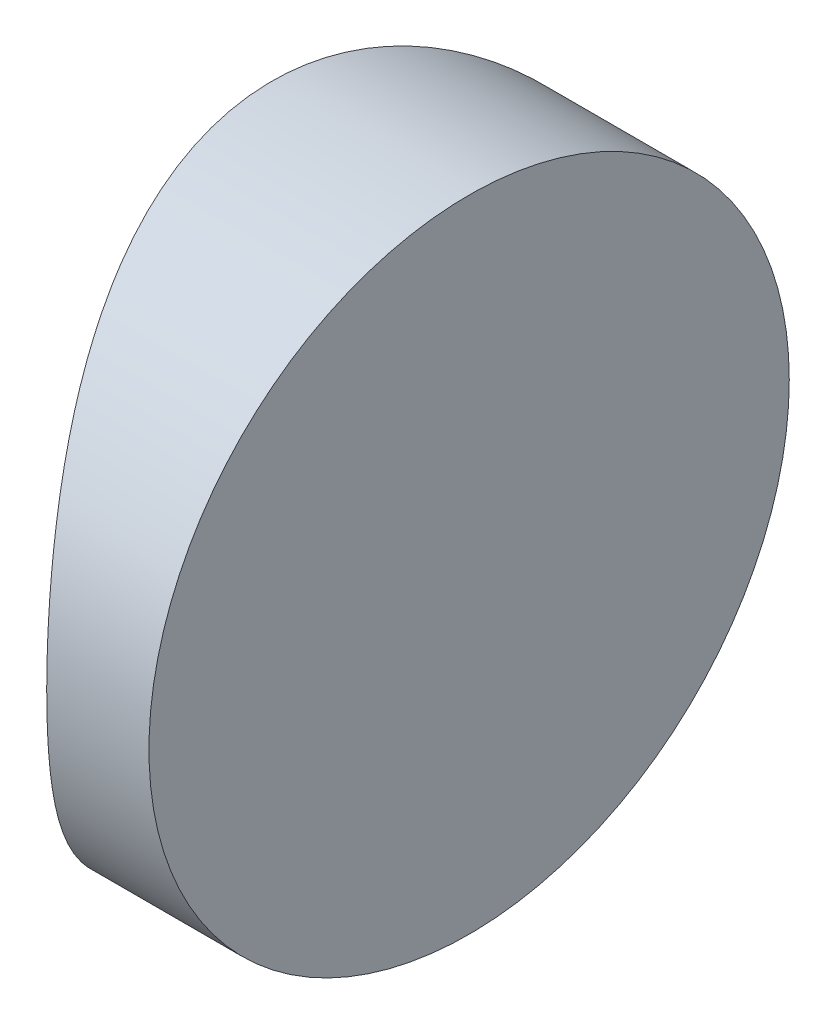
SolidWorks part; units mm, degrees
ref_plane "前视基准面" through (0, 0, 0) normal (0, 0, 1) x (1, 0, 0)
ref_plane "上视基准面" through (0, 0, 0) normal (0, 1, 0) x (1, 0, 0)
ref_plane "右视基准面" through (0, 0, 0) normal (1, 0, 0) x (0, 0, -1)
sketch "草图1" plane through (0, 0, 0) normal (0, 1, 0) x (1, 0, 0)
  line L0 (10.7432, 0) -> (-19.1624, 0) construction
  line L1 (-5.2505, 6.25) -> (-3.2548, 6.25)
  line L2 (-5.2505, -6.25) -> (-3.2548, -6.25)
  line L3 (-3.2548, 6.25) -> (-3.2548, -6.25)
  arc A0 (-5.2505, 6.25) -> (-5.2505, -6.25) centre (4.3552, 0) ccw
  point P19 (-7.1048, 0)
  point P20 (-3.2548, 0)
  dimension "D2" = 6.25
  dimension "D3" = 11.46
  dimension "D4" = 3.85
  dimension "D1" = 6.25
extrude "凸台-拉伸1" add sketch "草图1" along normal blind 12.5 contours A0 L2 L3 L1
sketch "草图2" plane through (-3.2548, 0, 0) normal (1, 0, 0) x (0, 0, -1)
  line L0 (6.25, 0) -> (-6.25, 0) construction
  line L7 (-6.25, 0) -> (6.25, 0)
  line L8 (6.25, 0) -> (6.25, 12.5)
  line L9 (6.25, 12.5) -> (-6.25, 12.5)
  line L10 (-6.25, 12.5) -> (-6.25, 0)
  line L11 (-6.25, 0) -> (6.25, 0)
  line L12 (6.25, 0) -> (6.25, 12.5)
  line L13 (6.25, 12.5) -> (-6.25, 12.5)
  line L14 (-6.25, 12.5) -> (-6.25, 0)
  circle A0 centre (0, 6.25) radius 6.25
  line M1 (-6.25, 0) -> (6.25, 0)
  line M2 (6.25, 0) -> (6.25, 12.5)
  line M3 (6.25, 12.5) -> (-6.25, 12.5)
  line M4 (-6.25, 12.5) -> (-6.25, 0)
  dimension "D1" = 12.5
  dimension "D2" = 6.25
  dimension "D3" = 0
extrude "切除-拉伸8" cut sketch "草图2" against normal blind 12.7 contours A0 L13 M4 | A0 L12 M3 | A0 L11 M2 | A0 L14 M1
